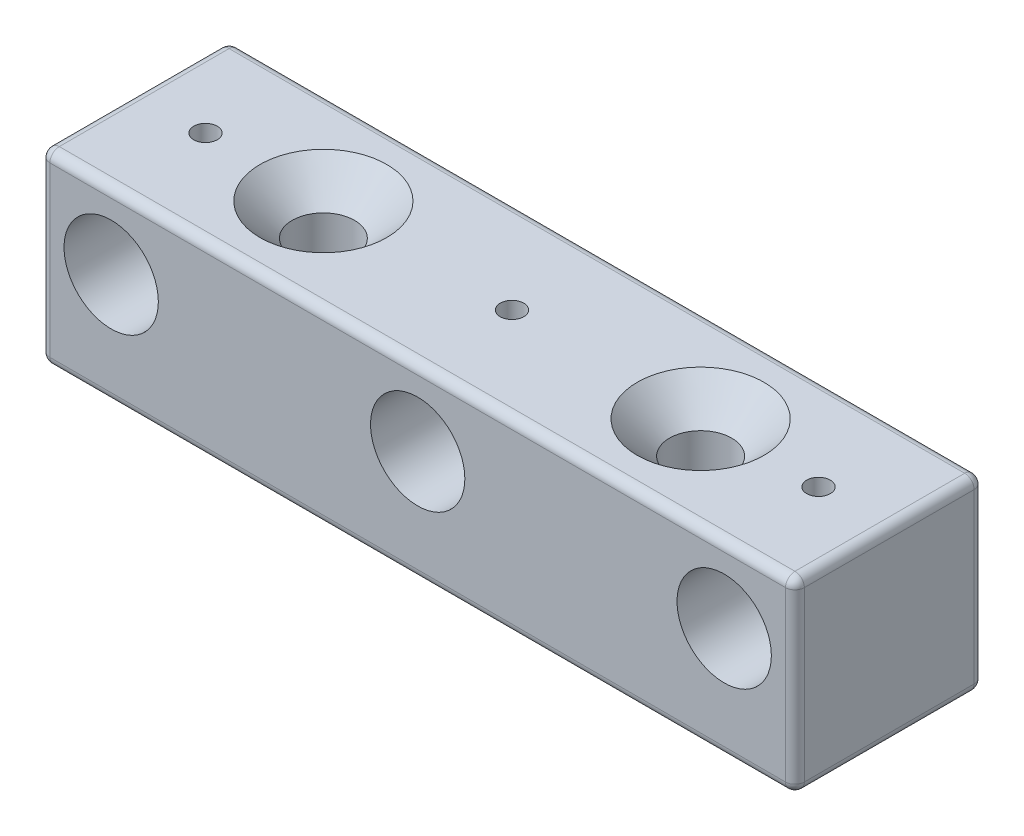
SolidWorks part; units mm, degrees
ref_plane "Front Plane" through (0, 0, 0) normal (0, 0, 1) x (1, 0, 0)
ref_plane "Top Plane" through (0, 0, 0) normal (0, 1, 0) x (1, 0, 0)
ref_plane "Right Plane" through (0, 0, 0) normal (1, 0, 0) x (0, 0, -1)
sketch "Sketch1" plane through (0, 0, 0) normal (0, 1, 0) x (1, 0, 0)
  line L1 (0, 0) -> (80, 0)
  line L2 (0, 0) -> (0, 20)
  line L3 (0, 20) -> (80, 20)
  line L4 (80, 0) -> (80, 20)
  line L5 (0, 0) -> (80, 20) construction
  line L6 (0, 20) -> (80, 0) construction
  point P4 (40, 10)
  dimension "D1" = 80
  dimension "D2" = 20
extrude "Boss-Extrude1" add sketch "Sketch1" along normal blind 19.85
sketch "Sketch2" plane through (0, 19.85, 0) normal (0, 1, 0) x (1, 0, 0)
  line L0 (0, 10) -> (80, 10) construction
  line L1 (0, 20) -> (0, 0) construction
  line L2 (80, 0) -> (80, 20) construction
  circle A0 centre (20, 10) radius 3.1
  circle A1 centre (60, 10) radius 3.1
  point P14 (40, 10)
  dimension "D2" = 6.2
  dimension "D1" = 40
  dimension "D3" = 20
extrude "Cut-Extrude1" cut sketch "Sketch2" against normal up to next
sketch "Sketch3" plane through (0, 0, 0) normal (0, 0, 1) x (1, 0, 0)
  line L0 (0, 19.85) -> (80, 19.85) construction
  line L1 (0, 19.85) -> (0, 0) construction
  line L2 (80, 19.85) -> (80, 0) construction
  line L3 (40, 0) -> (40, 19.85) construction
  line L4 (0, 0) -> (80, 0) construction
  circle A0 centre (7.5, 11.85) radius 5
  circle A1 centre (72.5, 11.85) radius 5
  circle A2 centre (40, 11.85) radius 5
  dimension "D1" = 10
  dimension "D2" = 7.5
  dimension "D3" = 7.5
  dimension "D4" = 8
extrude "Cut-Extrude2" cut sketch "Sketch3" against normal up to next contours A0 | A1 | A2
fillet "Fillet1" radius 1 12 edges at (80, 9.925, -20) (80, 9.925, 0) (0, 9.925, 0) (0, 9.925, -20) (0, 0, -10) (40, 0, -20) (80, 0, -10) (40, 0, 0) (80, 19.85, -10) (40, 19.85, 0) (40, 19.85, -20) (0, 19.85, -10)
hole_wizard "CSK for M6 SFHCS1" positions "Sketch4" profile "Sketch5" countersink size "M6" standard "Autoliv NAM Metric" end condition up to next
sketch "Sketch4" plane through (0, 19.85, 0) normal (0, 1, 0) x (1, 0, 0)
  point P0 (60, 10)
  point P3 (20, 10)
sketch "Sketch5" plane through (60, 19.85, -10) normal (1, 0, 0) x (0, 0, 1)
  line L0 (0, 0) -> (0, 19.85)
  line L1 (0, 19.85) -> (3.3, 19.85)
  line L2 (3.3, 19.85) -> (3.3, 3.42)
  line L3 (3.3, 3.42) -> (6.72, 0)
  line L5 (6.72, 0) -> (0, 0)
  line L6 (-3.3, 3.42) -> (-6.72, 0) construction
  line L11 (0, -6.35) -> (0, 107.95) construction
  dimension "Thru Hole Dia." = 6.6
  dimension "Thru Hole Depth" = 19.85
  dimension "Near C'Sink Dia." = 13.44
  dimension "Near C'Sink Angle" = 90
sketch "Sketch6" plane through (0, 19.85, 0) normal (0, 1, 0) x (1, 0, 0)
  line L0 (67.5, 0) -> (77.5, 0) construction
  line L1 (35, 0) -> (45, 0) construction
  line L2 (2.5, 0) -> (12.5, 0) construction
  line L3 (67.5, 0) -> (77.5, 0) construction
  line L4 (35, 0) -> (45, 0) construction
  line L5 (2.5, 0) -> (12.5, 0) construction
  line L6 (77.5, 20) -> (67.5, 20) construction
  line L7 (77.5, 20) -> (67.5, 20) construction
  line L8 (12.5, 20) -> (2.5, 20) construction
  line L9 (12.5, 20) -> (2.5, 20) construction
  line L10 (45, 20) -> (35, 20) construction
  line L11 (45, 20) -> (35, 20) construction
  line L12 (7.5, 0) -> (7.5, 20) construction
  line L13 (40, 0) -> (40, 20) construction
  line L14 (72.5, 0) -> (72.5, 20) construction
  line L15 (79, 10) -> (1, 10) construction
  line L16 (79, 1) -> (79, 19) construction
  line L17 (1, 19) -> (1, 1) construction
  point P24 (7.5, 10)
  point P25 (40, 10)
  point P26 (72.5, 10)
hole_wizard "M3x0.5 Tapped Hole1" positions "Sketch7" profile "Sketch9" tap size "M3x0.5" standard "Autoliv NAM Metric"
sketch "Sketch7" plane through (0, 19.85, 0) normal (0, 1, 0) x (1, 0, 0)
  point P0 (7.5, 10)
  point P3 (40, 10)
  point P6 (72.5, 10)
sketch "Sketch9" plane through (7.5, 19.85, -10) normal (1, 0, 0) x (0, 0, 1)
  line L0 (0, 0) -> (0, 3)
  line L1 (0, 3) -> (1.25, 3)
  line L2 (1.25, 3) -> (1.25, 0)
  line L5 (1.25, 0) -> (0, 0)
  line L11 (0, -6.35) -> (0, 107.95) construction
  dimension "Thru Tap Drill Dia." = 2.5
  dimension "Thru Tap Drill Depth" = 3
cosmetic thread "Hole Thread1" parameters "D2"=3
cosmetic thread "Hole Thread2" parameters "D2"=3
cosmetic thread "Hole Thread3" parameters "D2"=3
